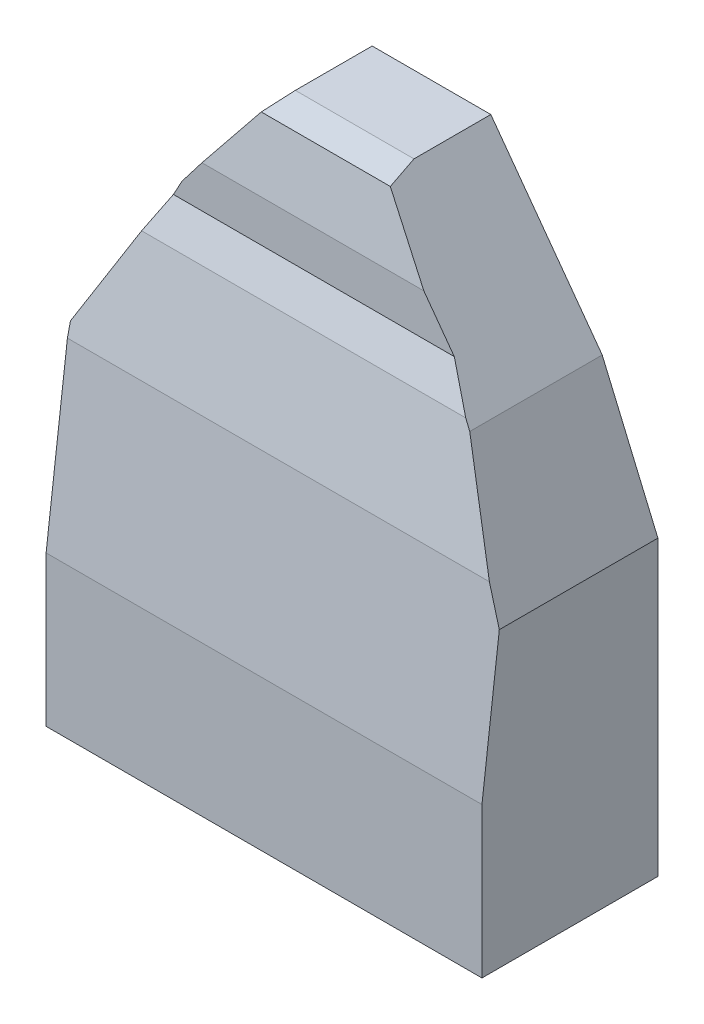
SolidWorks part; units mm, degrees
ref_plane "Front Plane" through (0, 0, 0) normal (0, 0, 1) x (1, 0, 0)
ref_plane "Top Plane" through (0, 0, 0) normal (0, 1, 0) x (1, 0, 0)
ref_plane "Right Plane" through (0, 0, 0) normal (1, 0, 0) x (0, 0, -1)
sketch "Sketch1" plane through (0, 0, 0) normal (0, 0, 1) x (1, 0, 0)
  line L0 (0, 0) -> (576.3025, 0)
  line L1 (576.3025, 0) -> (576.3025, 387.4034)
  line L2 (576.3025, 387.4034) -> (502.6639, 560.2941)
  line L3 (502.6639, 560.2941) -> (355.3866, 762)
  line L4 (355.3866, 762) -> (198.5042, 762)
  line L5 (198.5042, 762) -> (102.4538, 637.1345)
  line L6 (102.4538, 637.1345) -> (0, 448.2353)
  line L7 (0, 448.2353) -> (0, 0)
  point P10 (1.4991, 0)
  dimension "D1" = 762
extrude "Boss-Extrude1" add sketch "Sketch1" along normal blind 101.6
sketch "Sketch2" plane through (0, 0, 0) normal (-1, 0, 0) x (0, 0, 1)
  line L0 (101.6, 0) -> (232.6217, 0)
  line L1 (232.6217, 0) -> (232.6217, 198.6482)
  line L2 (232.6217, 198.6482) -> (204.4518, 430.5066)
  line L3 (204.4518, 430.5066) -> (172.7805, 570.8119)
  line L4 (172.7805, 570.8119) -> (155.0893, 615.7047)
  line L5 (155.0893, 615.7047) -> (155.0893, 670.9083)
  line L6 (155.0893, 670.9083) -> (139.6079, 752.7874)
  line L8 (139.6079, 752.7874) -> (101.6, 762)
  line L9 (101.6, 762) -> (101.6, 0)
  point P9 (135.2678, 752.8943)
  point P12 (178.1677, 515.2495)
  point P13 (150.7492, 671.0152)
  point P14 (168.4404, 570.9188)
  point P15 (200.1117, 430.6135)
  point P16 (97.2599, 762.1069)
  point P20 (96.2764, 764.3431)
  dimension "D1" = 0
  dimension "D2" = 0
extrude "Boss-Extrude2" add sketch "Sketch2" against normal up to surface (576.3025 mm away) up to face at (576.3025, 193.7017, 50.8)
sketch "Sketch3" plane through (0, 0, 101.6) normal (0, 0, -1) x (-1, 0, 0)
  line L0 (0, 448.2353) -> (-102.0796, 636.4445)
  line L1 (0, 448.2353) -> (-102.4538, 637.1345) construction
  line L2 (-102.0796, 636.4445) -> (-205.0523, 770.5126)
  line L3 (-102.4538, 637.1345) -> (-198.5042, 762) construction
  line L4 (-205.0523, 770.5126) -> (-205.0523, 987.3428)
  line L5 (-205.0523, 987.3428) -> (227.8795, 941.9217)
  line L6 (227.8795, 941.9217) -> (179.7159, 482.8494)
  line L7 (179.7159, 482.8494) -> (0, 448.2353)
  point P5 (-205.4812, 770.1827)
extrude "Cut-Extrude1" cut sketch "Sketch3" against normal through all
sketch "Sketch4" plane through (0, 0, 101.6) normal (0, 0, -1) x (-1, 0, 0)
  line L0 (-576.3025, 387.4034) -> (-502.6639, 560.2941)
  line L1 (-502.6639, 560.2941) -> (-355.3866, 762)
  line L2 (-355.3866, 762) -> (-386.6478, 961.5261)
  line L3 (-386.6478, 961.5261) -> (-935.091, 961.5261)
  line L4 (-935.091, 961.5261) -> (-884.9139, 472.9491)
  line L5 (-884.9139, 472.9491) -> (-576.3025, 387.4034)
extrude "Cut-Extrude2" cut sketch "Sketch4" against normal through all
